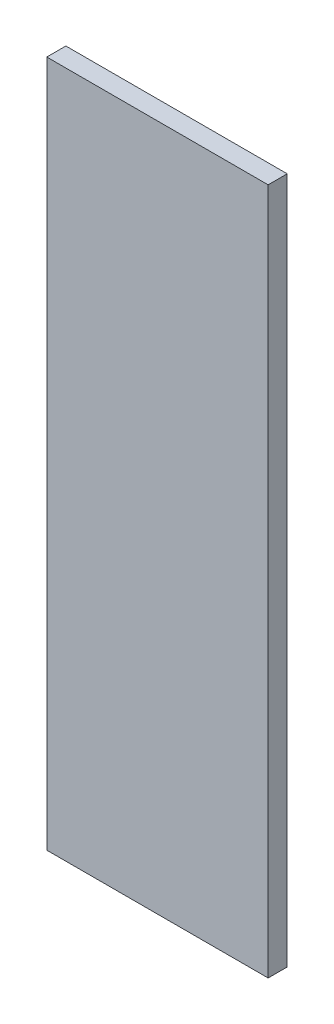
SolidWorks part; units mm, degrees
ref_plane "Plan de face" through (0, 0, 0) normal (0, 0, 1) x (1, 0, 0)
ref_plane "Plan de dessus" through (0, 0, 0) normal (0, 1, 0) x (1, 0, 0)
ref_plane "Plan de droite" through (0, 0, 0) normal (1, 0, 0) x (0, 0, -1)
sketch "Esquisse1" plane through (0, 0, 0) normal (0, 0, 1) x (1, 0, 0)
  line L0 (0, 0) -> (0, 180)
  line L1 (0, 180) -> (58, 180)
  line L2 (58, 180) -> (58, 0)
  line L3 (58, 0) -> (0, 0)
extrude "Boss.-Extru.2" add sketch "Esquisse1" along normal blind 5
